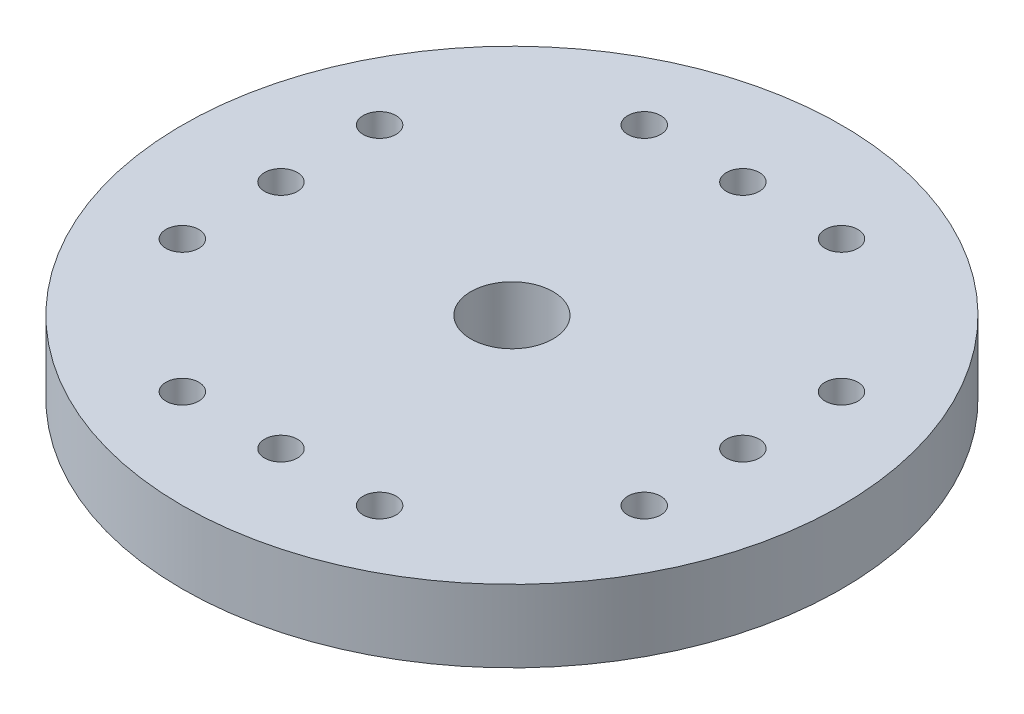
SolidWorks part; units mm, degrees
ref_plane "Front Plane" through (0, 0, 0) normal (0, 0, 1) x (1, 0, 0)
ref_plane "Top Plane" through (0, 0, 0) normal (0, 1, 0) x (1, 0, 0)
ref_plane "Right Plane" through (0, 0, 0) normal (1, 0, 0) x (0, 0, -1)
sketch "Sketch1" plane through (0, 0, 0) normal (0, 1, 0) x (1, 0, 0)
  circle A0 centre (0, 0) radius 10.025
  dimension "D1" = 20.05
extrude "Boss-Extrude1" add sketch "Sketch1" along normal blind 2.2
sketch "Sketch2" plane through (0, 0, 0) normal (0, -1, 0) x (1, 0, 0)
  line L0 (0, 0) -> (-10.025, 0) construction
  line L1 (-10.025, 0) -> (-7.025, 0) construction
  line L2 (-7.025, -3) -> (-7.025, 3) construction
  circle A0 centre (0, 0) radius 10.025 construction
  circle A1 centre (-7.025, -3) radius 0.5
  circle A2 centre (-7.025, 0) radius 0.5
  circle A3 centre (-7.025, 3) radius 0.5
  circle A4 centre (-3, 7.025) radius 0.5
  circle A5 centre (0, 7.025) radius 0.5
  circle A6 centre (3, 7.025) radius 0.5
  circle A7 centre (7.025, 3) radius 0.5
  circle A8 centre (7.025, 0) radius 0.5
  circle A9 centre (7.025, -3) radius 0.5
  circle A10 centre (3, -7.025) radius 0.5
  circle A11 centre (0, -7.025) radius 0.5
  circle A12 centre (-3, -7.025) radius 0.5
  point P10 (-7.025, 0)
  point P34 (0, 0)
  dimension "D3" = 1
  dimension "D4" = 1
  dimension "D5" = 1
  dimension "D1" = 3
  dimension "D2" = 6
  dimension "D6" = 4
extrude "Cut-Extrude1" cut sketch "Sketch2" against normal through all
sketch "Sketch3" plane through (0, 0, 0) normal (0, -1, 0) x (-1, 0, 0)
  circle A0 centre (0, 0) radius 3.8
  dimension "D1" = 7.6
extrude "Boss-Extrude2" add sketch "Sketch3" along normal blind 3.4
sketch "Sketch4" plane through (0, -3.4, 0) normal (0, -1, 0) x (1, 0, 0)
  circle A0 centre (0, 0) radius 3
  dimension "D1" = 6
extrude "Cut-Extrude2" cut sketch "Sketch4" against normal blind 2.8
sketch "Sketch5" plane through (0, -0.6, 0) normal (0, -1, 0) x (1, 0, 0)
  circle A0 centre (0, 0) radius 1.25
  dimension "D1" = 2.5
extrude "Cut-Extrude3" cut sketch "Sketch5" against normal through all
